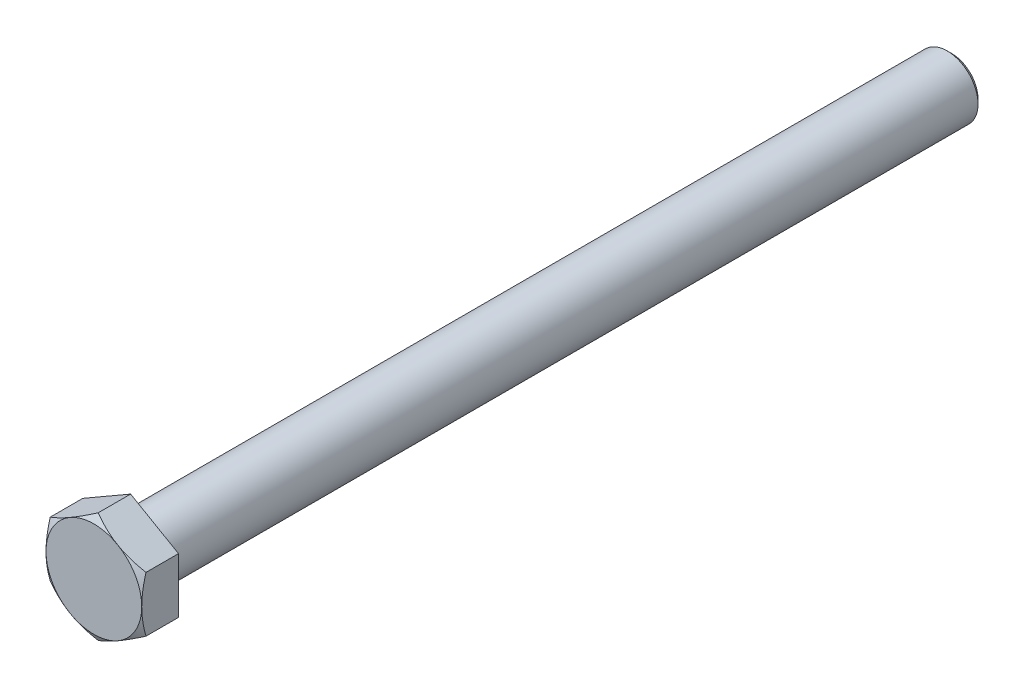
SolidWorks part; units mm, degrees
ref_plane "Front Plane" through (0, 0, 0) normal (0, 0, 1) x (1, 0, 0)
ref_plane "Top Plane" through (0, 0, 0) normal (0, 1, 0) x (1, 0, 0)
ref_plane "Right Plane" through (0, 0, 0) normal (1, 0, 0) x (0, 0, -1)
sketch "Sketch1" plane through (0, 0, 0) normal (0, 0, 1) x (1, 0, 0)
  line L0 (0, 0) -> (0, 10.7791) construction
  line L2 (0, 10.7791) -> (-9.335, 5.3896)
  line L3 (-9.335, 5.3896) -> (-9.335, -5.3896)
  line L4 (-9.335, -5.3896) -> (0, -10.7791)
  line L5 (0, -10.7791) -> (9.335, -5.3896)
  line L6 (9.335, -5.3896) -> (9.335, 5.3896)
  line L7 (9.335, 5.3896) -> (0, 10.7791)
  circle A0 centre (0, 0) radius 9.335 construction
  dimension "HEX" = 18.67
extrude "Boss-Extrude1" add sketch "Sketch1" along normal blind 7.32
sketch "Sketch2" plane through (0, 0, 0) normal (1, 0, 0) x (0, 0, -1)
  line L0 (0, 0) -> (160, 0) construction
  line L1 (0, 0) -> (0, 6.6)
  line L4 (159.1, 6) -> (160, 5.1)
  line L7 (160, 5.1) -> (160, 0)
  line L8 (160, 0) -> (0, 0)
  line L9 (159.1, 6) -> (0.6, 6)
  arc A3 (0.6, 6) -> (0, 6.6) centre (0.6, 6.6) cw
  dimension "D1" = 0.6
  dimension "LENGTH" = 160
  dimension "WIDTH2" = 10.2
  dimension "WIDTH1" = 12
  dimension "D5" = 45
revolve "Revolve1" add sketch "Sketch2" angle 360 about L0
cosmetic thread "Cosmetic Thread1" parameters "D1"=70, "D2"=12
sketch "Sketch3" plane through (0, 0, 0) normal (1, 0, 0) x (0, 0, -1)
  line L0 (-12.2049, 0) -> (129.7862, 0) construction
  line L1 (-7.32, 10.7791) -> (-6.4862, 10.7791)
  line L2 (-0.15, 10.7791) -> (-0.15, 8.7866)
  line L3 (-6.4862, 10.7791) -> (-7.32, 9.335)
  line L4 (-0.15, 8.7866) -> (0, 8.7)
  line L5 (-7.32, 9.335) -> (-7.32, 10.7791)
  line L6 (0, -5.3896) -> (0, 5.3896) construction
  line L7 (-7.32, 10.7791) -> (0, 10.7791) construction
  line L8 (-7.32, 5.3896) -> (-7.32, 10.7791) construction
  line L10 (0, 8.7) -> (0, 10.7791)
  line L11 (0, 10.7791) -> (-0.15, 10.7791)
  dimension "D1" = 30
  dimension "SAME AS HEX" = 18.67
  dimension "D3" = 30
  dimension "C" = 0.15
  dimension "DW" = 17.4
revolve "Cut-Revolve1" cut sketch "Sketch3" angle 360 about L0
